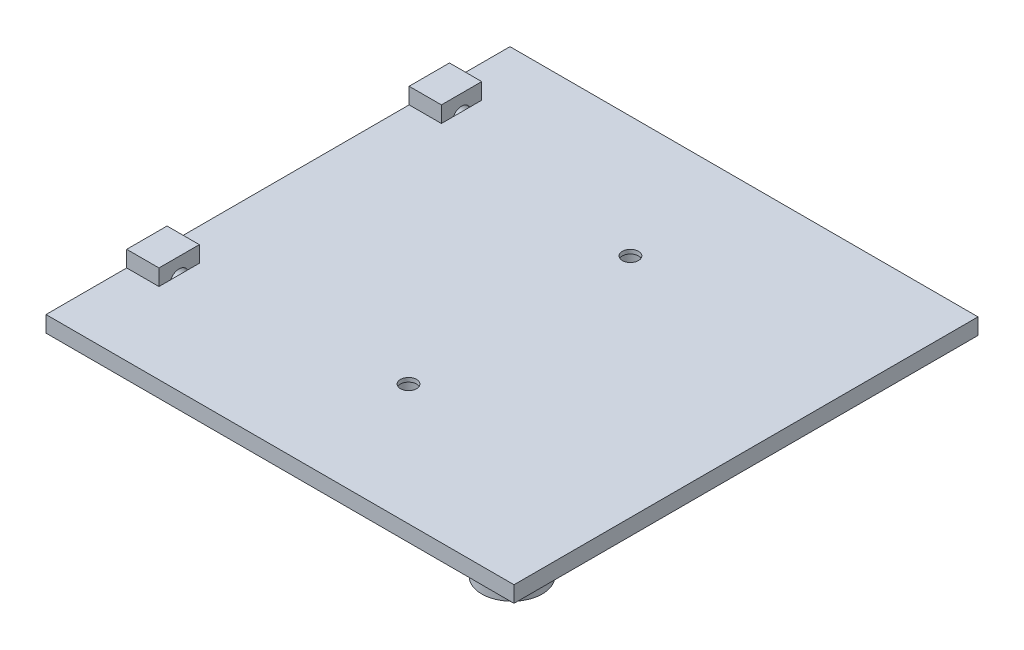
SolidWorks part; units mm, degrees
ref_plane "Front Plane" through (0, 0, 0) normal (0, 0, 1) x (1, 0, 0)
ref_plane "Top Plane" through (0, 0, 0) normal (0, 1, 0) x (1, 0, 0)
ref_plane "Right Plane" through (0, 0, 0) normal (1, 0, 0) x (0, 0, -1)
sketch "Sketch1" plane through (0, 0, 0) normal (0, 1, 0) x (1, 0, 0)
  line L1 (-93.2831, 34.3976) -> (22.7169, 34.3976)
  line L2 (-93.2831, 34.3976) -> (-93.2831, -80.6024)
  line L3 (-93.2831, -80.6024) -> (22.7169, -80.6024)
  line L4 (22.7169, 34.3976) -> (22.7169, -80.6024)
  dimension "D1" = 115
  dimension "D2" = 116
extrude "Boss-Extrude1" add sketch "Sketch1" along normal blind 4
sketch "Sketch2" plane through (0, 0, 0) normal (0, 1, 0) x (1, 0, 0)
  line L0 (-93.2831, 34.3976) -> (-93.2831, -80.6024) construction
  line L2 (22.7169, 34.3976) -> (-93.2831, 34.3976) construction
  circle A0 centre (14.2169, -72.6024) radius 7.5
  circle A1 centre (14.2169, -72.6024) radius 5
  dimension "D1" = 15
  dimension "D2" = 10
  dimension "D3" = 107.5
  dimension "D4" = 107
extrude "Boss-Extrude2" add sketch "Sketch2" against normal blind 2.5
ref_plane "Plane1" through (-93.2831, 0, 0) normal (-1, 0, 0) x (0, 0, 1)
sketch "Sketch3" plane through (-93.2831, 0, 0) normal (-1, 0, 0) x (0, 0, 1)
  line L10 (-34.3976, 4) -> (80.6024, 4) construction
  line L12 (-19.3976, 4) -> (-9.3976, 4)
  line L13 (-19.3976, 4) -> (-19.3976, 8)
  line L14 (-19.3976, 8) -> (-9.3976, 8)
  line L15 (-9.3976, 4) -> (-9.3976, 8)
  line L16 (50.6024, 4) -> (60.6024, 4)
  line L17 (50.6024, 4) -> (50.6024, 8)
  line L18 (50.6024, 8) -> (60.6024, 8)
  line L19 (60.6024, 4) -> (60.6024, 8)
  dimension "D7" = 4
  dimension "D8" = 10
  dimension "D10" = 4
  dimension "D11" = 10
extrude "Boss-Extrude3" add sketch "Sketch3" against normal blind 8
sketch "Sketch4" plane through (0, 4, 0) normal (0, 1, 0) x (1, 0, 0)
  line L0 (22.7169, -80.6024) -> (22.7169, 34.3976) construction
  line L1 (-77.2831, 28.3976) -> (7.7169, 28.3976)
  line L2 (-77.2831, 28.3976) -> (-77.2831, -75.6024)
  line L3 (-77.2831, -75.6024) -> (7.7169, -75.6024)
  line L4 (7.7169, 28.3976) -> (7.7169, -75.6024)
  line L5 (-93.2831, -80.6024) -> (22.7169, -80.6024) construction
  line L7 (-79.2831, 30.3976) -> (9.7169, 30.3976)
  line L8 (-79.2831, 30.3976) -> (-79.2831, -77.6024)
  line L9 (-79.2831, -77.6024) -> (9.7169, -77.6024)
  line L10 (9.7169, 30.3976) -> (9.7169, -77.6024)
  dimension "D1" = 85
  dimension "D2" = 104
  dimension "D3" = 15
  dimension "D4" = 5
  dimension "D5" = 89
  dimension "D6" = 108
  dimension "D7" = 2
  dimension "D8" = 2
extrude "Boss-Extrude4" [suppressed] add sketch "Sketch4" along normal blind 3
sketch "Sketch5" [suppressed] plane through (0, 3, 0) normal (0, 1, 0) x (1, 0, 0)
  line L0 (16.2169, 30.3976) -> (-72.7831, 30.3976) construction
  line L1 (16.2169, 30.3976) -> (-72.7831, 30.3976) construction
  line L2 (-72.7831, 30.3976) -> (-72.7831, -77.6024) construction
  line L3 (16.2169, -77.6024) -> (16.2169, 30.3976) construction
  circle A0 centre (-80.7831, -23.6024) radius 1.025
  circle A2 centre (24.2169, -23.6024) radius 1.025
  dimension "D1" = 2.05
  dimension "D2" = 2.05
  dimension "D3" = 54
  dimension "D4" = 54
  dimension "D5" = 8
  dimension "D6" = 8
extrude "Cut-Extrude1" [suppressed] cut sketch "Sketch5" against normal through all
sketch "Sketch6" plane through (-93.2831, 0, 0) normal (-1, 0, 0) x (0, 0, 1)
  line L0 (-34.3976, 0) -> (80.6024, 0) construction
  line L1 (-19.3976, 8) -> (-19.3976, 4) construction
  line L2 (50.6024, 8) -> (50.6024, 4) construction
  circle A0 centre (-14.3976, 3) radius 2.2256
  circle A1 centre (55.6024, 3) radius 2.3025
  dimension "D1" = 3
  dimension "D2" = 3
  dimension "D3" = 5
  dimension "D4" = 5
extrude "Cut-Extrude2" cut sketch "Sketch6" against normal blind 8
sketch "Sketch7" plane through (0, 0, 0) normal (0, -1, 0) x (1, 0, 0)
  line L2 (22.7169, 80.6024) -> (22.7169, -34.3976) construction
  line L3 (22.7169, -34.3976) -> (-93.2831, -34.3976) construction
  circle A0 centre (2.7169, -14.3976) radius 5
  dimension "D1" = 10
  dimension "D2" = 20
  dimension "D3" = 20
extrude "Boss-Extrude5" add sketch "Sketch7" along normal blind 3
sketch "Sketch9" plane through (0, 4, 0) normal (0, 1, 0) x (1, 0, 0)
  line L0 (22.7169, 34.3976) -> (-93.2831, 34.3976) construction
  circle A0 centre (-33.4296, 4.3976) radius 2
  circle A1 centre (-33.4296, -50.6024) radius 2
  dimension "D1" = 4
  dimension "D2" = 4
  dimension "D3" = 55
  dimension "D4" = 30
extrude "Cut-Extrude3" cut sketch "Sketch9" along normal through all both and the other way through all
sketch "Sketch10" plane through (0, 0, 0) normal (0, -1, 0) x (1, 0, 0)
  circle A0 centre (-33.4296, -4.3976) radius 3.5
  circle A2 centre (-33.4296, 50.6024) radius 3.5
  dimension "D1" = 7
  dimension "D2" = 7
extrude "Cut-Extrude5" cut sketch "Sketch10" against normal blind 3
